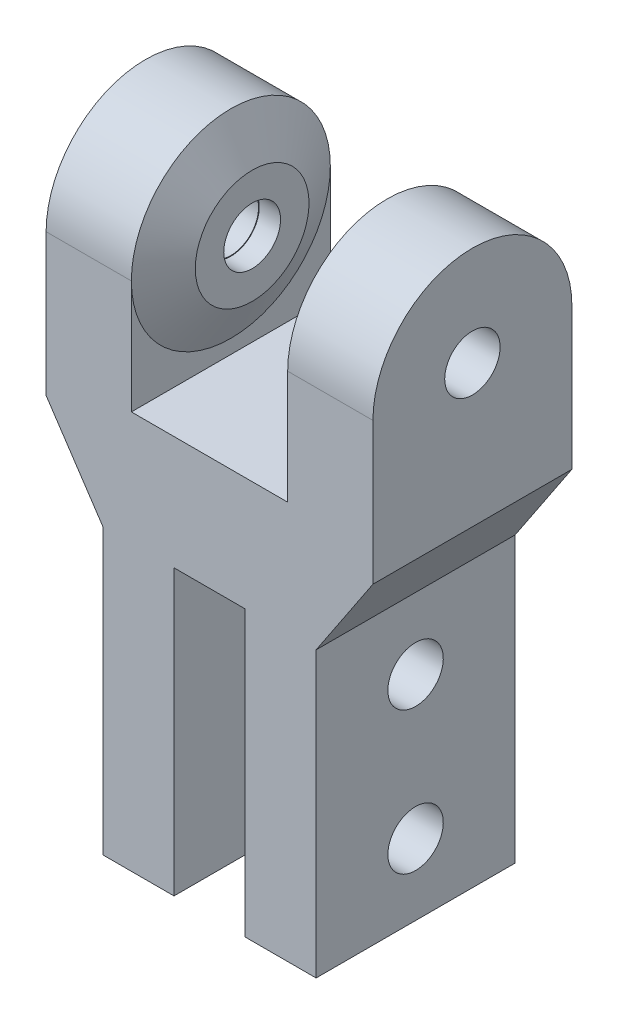
SolidWorks part; units mm, degrees
ref_plane "Front Plane" through (0, 0, 0) normal (0, 0, 1) x (1, 0, 0)
ref_plane "Top Plane" through (0, 0, 0) normal (0, 1, 0) x (1, 0, 0)
ref_plane "Right Plane" through (0, 0, 0) normal (1, 0, 0) x (0, 0, -1)
sketch "Sketch1" plane through (0, 0, 0) normal (0, 0, 1) x (1, 0, 0)
  line L0 (0, 5.1775) -> (0, -3.9429) construction
  line L1 (-1.25, -10) -> (-3.75, -10)
  line L2 (-3.75, -10) -> (-3.75, 0)
  line L3 (-4.25, 12) -> (-2.75, 12)
  line L4 (-2.75, 12) -> (-2.75, 4)
  line L5 (-2.75, 4) -> (2.75, 4)
  line L7 (1.25, 0) -> (-1.25, 0)
  line L8 (-1.25, 0) -> (-1.25, -10)
  line L9 (-3.75, 0) -> (-5.75, 3)
  line L10 (-5.75, 3) -> (-5.75, 12)
  line L11 (-5.75, 12) -> (-4.25, 12)
  line L12 (1.25, -10) -> (3.75, -10)
  line L13 (3.75, 0) -> (5.75, 3)
  line L14 (3.75, -10) -> (3.75, 0)
  line L15 (1.25, 0) -> (1.25, -10)
  line L16 (2.75, 12) -> (2.75, 4)
  line L17 (4.25, 12) -> (2.75, 12)
  line L18 (5.75, 12) -> (4.25, 12)
  line L19 (5.75, 3) -> (5.75, 12)
  point P19 (0, 0)
  point P20 (0, 4)
  dimension "D1" = 1.25
  dimension "D2" = 10
  dimension "D3" = 2.5
  dimension "D4" = 8
  dimension "D5" = 4
  dimension "D6" = 2.75
  dimension "D7" = 3
  dimension "D8" = 1
extrude "Boss-Extrude1" add sketch "Sketch1" along normal mid plane 7
sketch "Sketch2" plane through (0, 0, 0) normal (1, 0, 0) x (0, 0, -1)
  line L0 (-3.5, -10) -> (3.5, -10) construction
  line L1 (-3.5, 7.9912) -> (-3.5, 12)
  line L2 (-3.5, 12) -> (3.5, 12)
  line L3 (3.5, 12) -> (3.5, 7.9912)
  circle A0 centre (0, -2.5) radius 0.975
  circle A1 centre (0, -7.5) radius 0.975
  circle A2 centre (0, 7.9912) radius 0.975
  circle A4 centre (0, 7.9912) radius 3.5
  dimension "D1" = 1.95
  dimension "D2" = 1.95
  dimension "D3" = 1.95
  dimension "D4" = 2.5
  dimension "D5" = 5
extrude "Cut-Extrude1" cut sketch "Sketch2" against normal mid plane 15 contours A4 L3 L2 L1 | A2 | A0 | A1
ref_axis "Axis1" through (-5.75, 7.9912, 0) along (1, 0, 0)
sketch "Sketch3" plane through (0, 0, 0) normal (0, 0, 1) x (1, 0, 0)
  line L0 (-2.75, 8.9912) -> (-2, 8.9912)
  line L1 (-2.75, 7.9912) -> (-2.75, 11.4912) construction
  line L2 (-2, 8.9912) -> (-2, 9.9912)
  line L3 (-2, 9.9912) -> (-2.75, 11.4912)
  line L4 (0, -3.85) -> (0, 3.85) construction
  line L5 (-5.75, 7.9912) -> (-2.75, 7.9912) construction
  line L6 (-2.75, 8.9912) -> (-2.75, 11.4912)
  dimension "D1" = 2
  dimension "D2" = 1
  dimension "D3" = 1
revolve "Revolve1" add sketch "Sketch3" angle 360 about axis through (-5.75, 7.9912, 0) along (1, 0, 0)
mirror "Mirror1" about plane through (0, 0, 0) normal (1, 0, 0) of "Revolve1"
